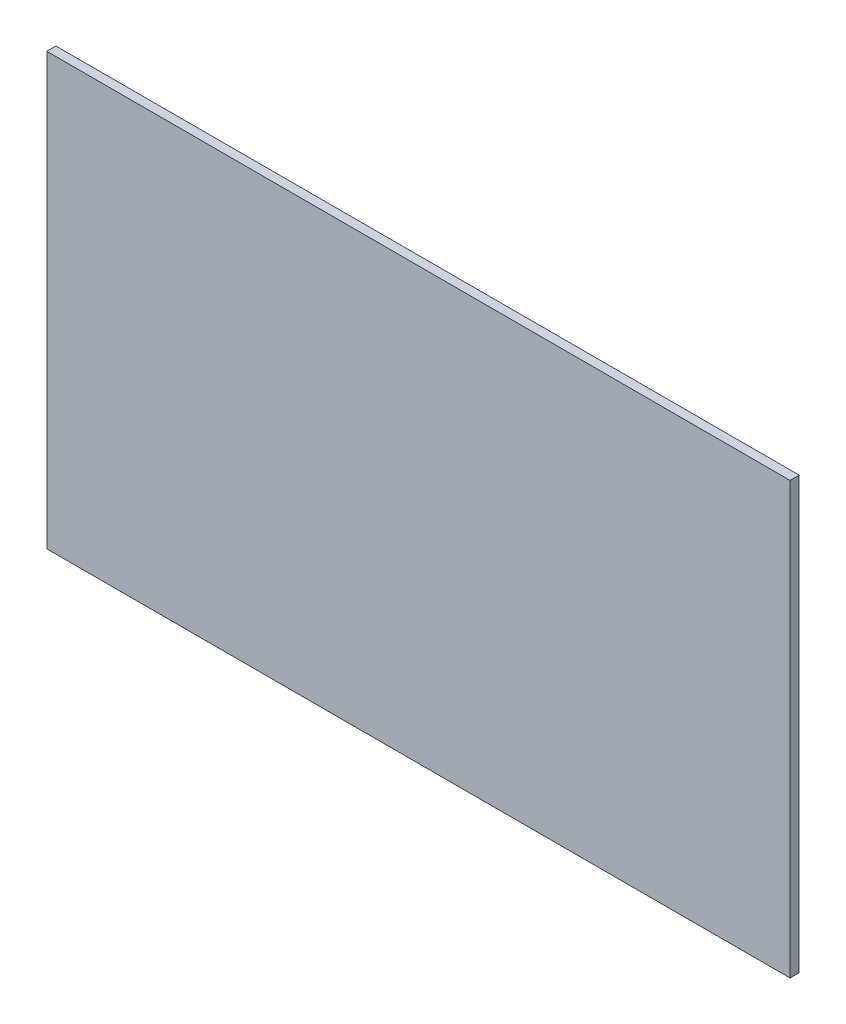
SolidWorks part; units mm, degrees
ref_plane "Front Plane" through (0, 0, 0) normal (0, 0, 1) x (1, 0, 0)
ref_plane "Top Plane" through (0, 0, 0) normal (0, 1, 0) x (1, 0, 0)
ref_plane "Right Plane" through (0, 0, 0) normal (1, 0, 0) x (0, 0, -1)
sketch "Sketch1" plane through (0, 0, 0) normal (0, 0, 1) x (1, 0, 0)
  line L0 (20, -22) -> (-525, -22) construction
  line L1 (4, -22) -> (-159, -22)
  line L2 (4, -22) -> (4, 77.5)
  line L3 (4, 77.5) -> (-159, 77.5)
  line L4 (-159, -22) -> (-159, 77.5)
  line L5 (4, 175) -> (4, -20) construction
  line L10 (4, 72.5) -> (-159, 72.5)
  line L11 (-159, 155) -> (-159, 0) construction
  point P8 (4, 77.5)
  dimension "D1" = 5
extrude "Boss-Extrude1" add sketch "Sketch1" along normal blind 2 contours L2 L10 L4 L1
